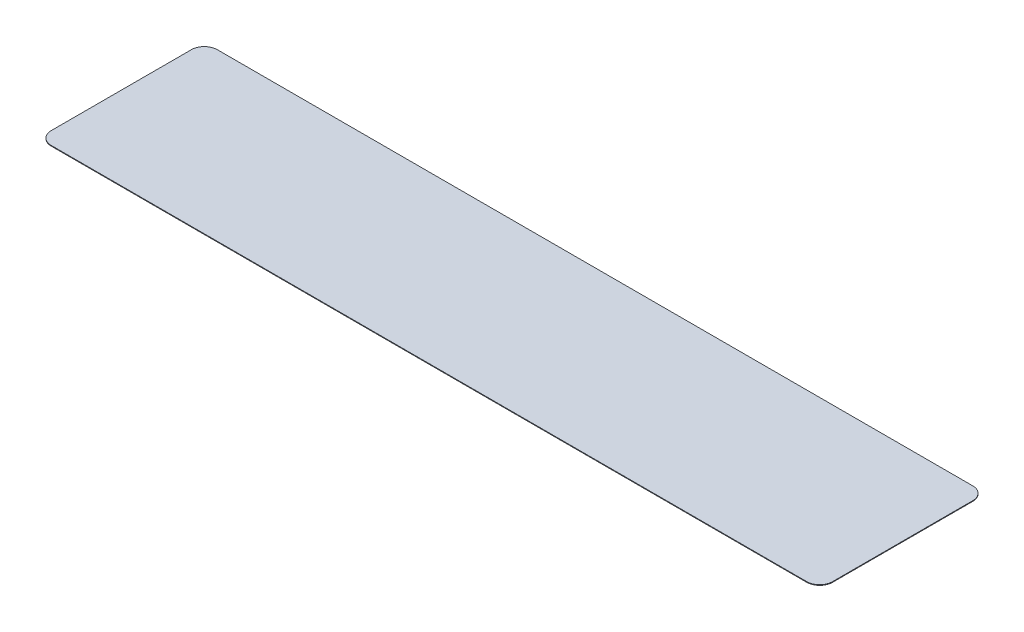
SolidWorks part; units mm, degrees
ref_plane "Front Plane" through (0, 0, 0) normal (0, 0, 1) x (1, 0, 0)
ref_plane "Top Plane" through (0, 0, 0) normal (0, 1, 0) x (1, 0, 0)
ref_plane "Right Plane" through (0, 0, 0) normal (1, 0, 0) x (0, 0, -1)
sketch "Sketch1" plane through (0, 0, 0) normal (0, 1, 0) x (1, 0, 0)
  line L0 (0, 23.7367) -> (0, -23.7367) construction
  line L1 (-44.5135, 9.779) -> (44.5135, 9.779)
  line L2 (-46.0375, 8.255) -> (-46.0375, -8.255)
  line L3 (-44.5135, -9.779) -> (44.5135, -9.779)
  line L4 (46.0375, 8.255) -> (46.0375, -8.255)
  line L5 (37.3634, 0) -> (-46.4478, 0) construction
  arc A0 (-44.5135, 9.779) -> (-46.0375, 8.255) centre (-44.5135, 8.255) ccw
  arc A1 (-44.5135, -9.779) -> (-46.0375, -8.255) centre (-44.5135, -8.255) cw
  arc A2 (46.0375, -8.255) -> (44.5135, -9.779) centre (44.5135, -8.255) cw
  arc A3 (46.0375, 8.255) -> (44.5135, 9.779) centre (44.5135, 8.255) ccw
  point P11 (-46.0375, 9.779)
  point P16 (46.0375, -9.779)
  point P19 (46.0375, 9.779)
  dimension "D3" = 1.524
  dimension "D1" = 92.075
  dimension "D2" = 19.558
extrude "Extrude2" add sketch "Sketch1" along normal blind 0.0762
